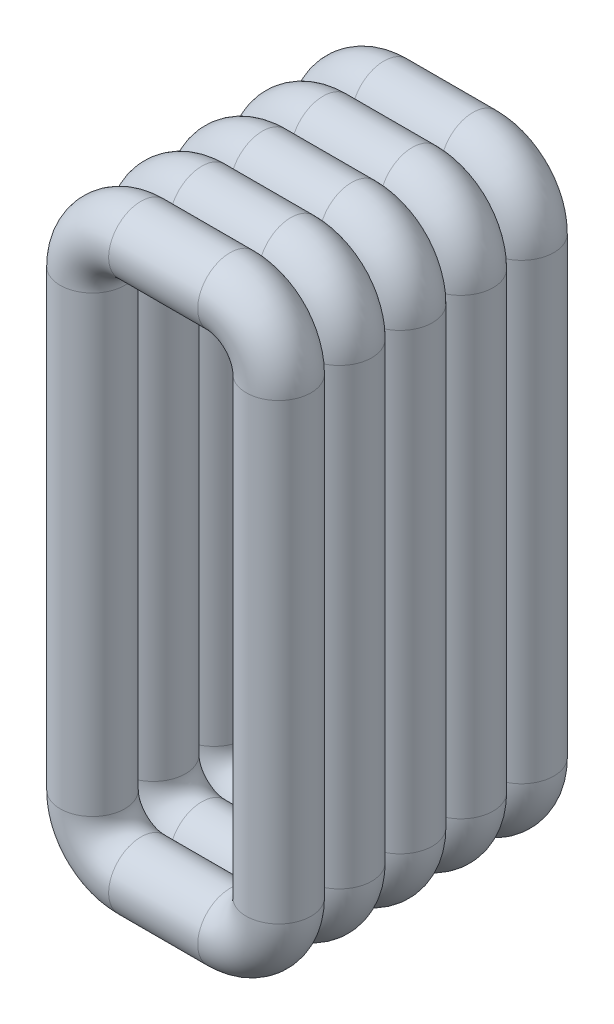
SolidWorks part; units mm, degrees
ref_plane "Plan de face" through (0, 0, 0) normal (0, 0, 1) x (1, 0, 0)
ref_plane "Plan de dessus" through (0, 0, 0) normal (0, 1, 0) x (1, 0, 0)
ref_plane "Plan de droite" through (0, 0, 0) normal (1, 0, 0) x (0, 0, -1)
sketch "Esquisse2" plane through (0, 0, 0) normal (1, 0, 0) x (0, 0, -1)
  circle A0 centre (0, 3.4) radius 0.4
  dimension "D1" = 0.8
  dimension "D2" = 3.4
sketch "Esquisse3" plane through (0, 0, 0) normal (0, 0, 1) x (1, 0, 0)
  line L1 (0.55, -3) -> (-0.55, -3)
  line L2 (0.75, -2.8) -> (0.75, 2.8)
  line L3 (0.55, 3) -> (-0.55, 3)
  line L4 (-0.75, -2.8) -> (-0.75, 2.8)
  line L5 (0.75, -3) -> (-0.75, 3) construction
  line L6 (0.75, 3) -> (-0.75, -3) construction
  arc A0 (-0.55, -3) -> (-0.75, -2.8) centre (-0.55, -2.8) cw
  arc A1 (0.55, -3) -> (0.75, -2.8) centre (0.55, -2.8) ccw
  arc A2 (0.75, 2.8) -> (0.55, 3) centre (0.55, 2.8) ccw
  arc A3 (-0.55, 3) -> (-0.75, 2.8) centre (-0.55, 2.8) ccw
  point P0 (0, 0)
  dimension "D3" = 0.2
  dimension "D1" = 6
  dimension "D2" = 1.5
sweep "Balayage1" add profiles "Esquisse2" path "Esquisse3"
pattern_linear "Répétition linéaire1" count 5 spacing 0.75 along (0, 0, 1) of "Balayage1"
